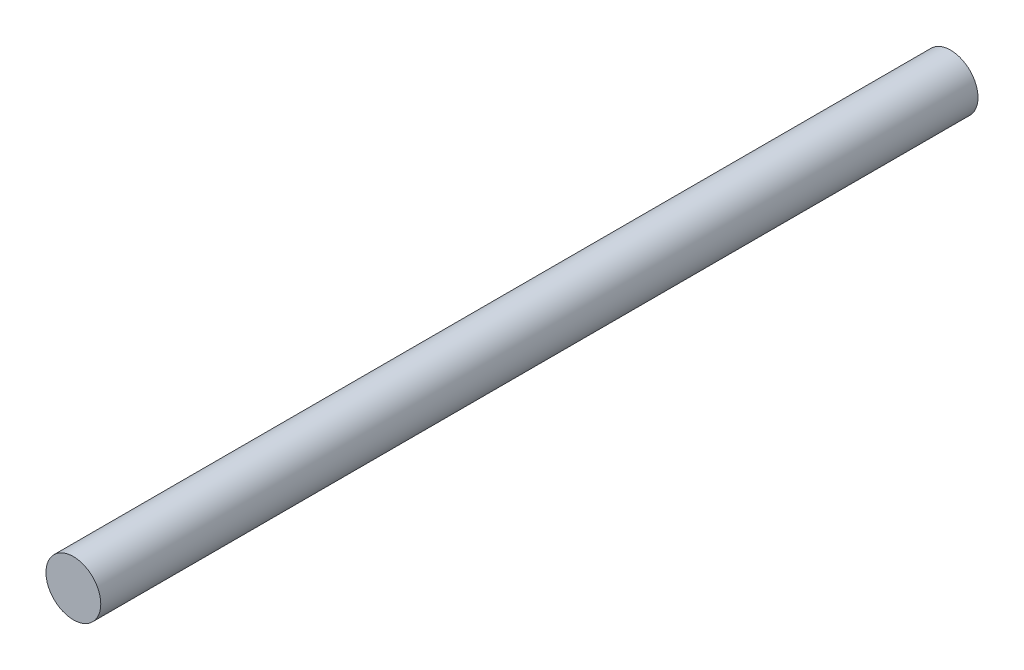
SolidWorks part; units mm, degrees
ref_plane "Front Plane" through (0, 0, 0) normal (0, 0, 1) x (1, 0, 0)
ref_plane "Top Plane" through (0, 0, 0) normal (0, 1, 0) x (1, 0, 0)
ref_plane "Right Plane" through (0, 0, 0) normal (1, 0, 0) x (0, 0, -1)
sketch "Sketch1" plane through (0, 0, 0) normal (0, 0, 1) x (1, 0, 0)
  circle A0 centre (-45.925, -30.3905) radius 5
extrude "Boss-Extrude1" add sketch "Sketch1" along normal blind 160 contours A0
